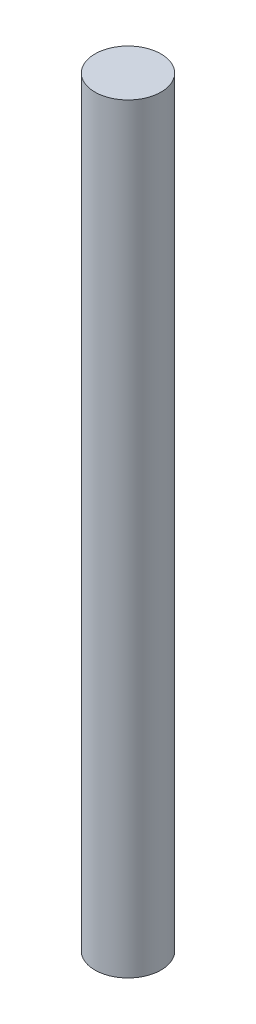
SolidWorks part; units mm, degrees
ref_plane "Front Plane" through (0, 0, 0) normal (0, 0, 1) x (1, 0, 0)
ref_plane "Top Plane" through (0, 0, 0) normal (0, 1, 0) x (1, 0, 0)
ref_plane "Right Plane" through (0, 0, 0) normal (1, 0, 0) x (0, 0, -1)
sketch "Sketch1" plane through (0, 0, 0) normal (0, 1, 0) x (1, 0, 0)
  circle A0 centre (0, 0) radius 1
  dimension "D1" = 2
extrude "Boss-Extrude1" add sketch "Sketch1" along normal blind 23
